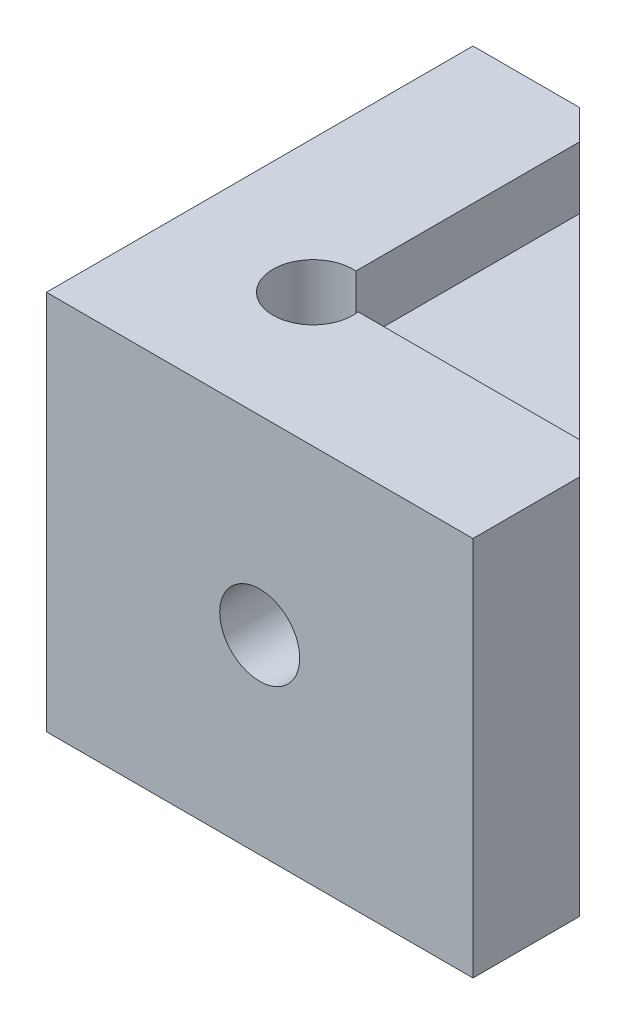
SolidWorks part; units mm, degrees
ref_plane "Front Plane" through (0, 0, 0) normal (0, 0, 1) x (1, 0, 0)
ref_plane "Top Plane" through (0, 0, 0) normal (0, 1, 0) x (1, 0, 0)
ref_plane "Right Plane" through (0, 0, 0) normal (1, 0, 0) x (0, 0, -1)
sketch "Sketch1" plane through (0, 0, 0) normal (0, 1, 0) x (1, 0, 0)
  line L1 (0, 0) -> (38.1, 0)
  line L5 (0, 0) -> (0, 38.1)
  line L6 (0, 38.1) -> (9.525, 38.1)
  line L7 (9.525, 38.1) -> (38.1, 9.525)
  line L8 (38.1, 9.525) -> (38.1, 0)
  dimension "D1" = 38.1
  dimension "D2" = 9.525
extrude "Main Body" add sketch "Sketch1" along normal blind 34
sketch "Sketch3" plane through (0, 0, 0) normal (0, 0, 1) x (1, 0, 0)
  line L0 (0, 0) -> (38.1, 34) construction
  circle A0 centre (19.05, 17) radius 3.5719
  circle A1 centre (19.05, 17) radius 7.9375 construction
  dimension "D1" = 7.1437
  dimension "D2" = 15.875
extrude "9/32 Right Rail" cut sketch "Sketch3" against normal blind 5.5562 and the other way through all
sketch "Sketch4" plane through (0, 0, 0) normal (-1, 0, 0) x (0, 0, 1)
  line L0 (0, 0) -> (-38.1, 34) construction
  circle A0 centre (-19.05, 17) radius 3.5719
  circle A1 centre (-19.05, 17) radius 7.9375 construction
  dimension "D1" = 7.1437
  dimension "D2" = 15.875
extrude "9/32 Left Rail" cut sketch "Sketch4" against normal blind 5.5562
sketch "Sketch8" plane through (0, 34, 0) normal (0, 1, 0) x (1, 0, 0)
  line L0 (0, 0) -> (23.8125, 23.8125) construction
  line L1 (38.1, 9.525) -> (9.525, 38.1) construction
  circle A0 centre (11.9062, 11.9062) radius 3.175 construction
  circle A1 centre (11.9062, 11.9062) radius 7.9375 construction
  circle A2 centre (11.9062, 11.9062) radius 3.5719
  dimension "D1" = 6.35
  dimension "D2" = 15.875
  dimension "D3" = 0.3969
extrude "9/32 Topper" cut sketch "Sketch8" against normal through all both and the other way through all
ref_plane "Plane1" through (5.5562, 0, 0) normal (-1, 0, 0) x (0, 0, 1)
sketch "Sketch9" plane through (0, 0, 0) normal (-1, 0, 0) x (0, 0, 1)
  line L0 (-19.05, 0) -> (-19.05, 34) construction
  line L1 (-12.6342, 17) -> (-15.8421, 22.5562) construction
  line L2 (-15.8421, 22.5562) -> (-22.2579, 22.5562) construction
  line L3 (-22.2579, 22.5562) -> (-25.4658, 17) construction
  line L4 (-25.4658, 17) -> (-22.2579, 11.4437) construction
  line L5 (-22.2579, 11.4437) -> (-15.8421, 11.4437) construction
  line L6 (-15.8421, 11.4437) -> (-12.6342, 17) construction
  line L7 (-38.1, 0) -> (0, 0) construction
  line L8 (-38.1, 34) -> (0, 34) construction
  line L9 (-22.3725, 22.7547) -> (-25.6949, 17)
  line L10 (-25.6949, 17) -> (-22.3725, 11.2453)
  line L11 (-22.3725, 11.2453) -> (-15.7275, 11.2453)
  line L12 (-15.7275, 11.2453) -> (-12.4051, 17)
  line L13 (-12.4051, 17) -> (-15.7275, 22.7547)
  line L14 (-15.7275, 22.7547) -> (-22.3725, 22.7547)
  line L15 (-38.1, 27.65) -> (-38.1, 6.35) construction
  line L16 (-38.1, 34) -> (-38.1, 0) construction
  line L17 (-38.1, 6.35) -> (-5.5562, 6.35) construction
  line L18 (-5.5562, 6.35) -> (-5.5562, 27.65) construction
  line L19 (-5.5562, 27.65) -> (-38.1, 27.65) construction
  line L20 (0, 34) -> (0, 0) construction
  circle A0 centre (-19.05, 17) radius 5.5563 construction
  point P15 (-19.05, 17)
  point P27 (-38.1, 17)
  point P29 (-38.1, 17)
  dimension "D1" = 11.1125
  dimension "D3" = 5.5562
  dimension "D4" = 6.35
  dimension "D2" = 0.1984
extrude "Cut-Extrude3" cut sketch "Sketch9" against normal up to surface (32.5438 mm away) from surface at -5.5563 up to face at (38.1, 17, -4.7625) starting at plane "Plane1"
ref_plane "Plane2" through (0, 0, -5.5563) normal (0, 0, 1) x (1, 0, 0)
sketch "Sketch10" plane through (0, 0, 0) normal (0, 0, 1) x (1, 0, 0)
  line L0 (19.05, 0) -> (19.05, 34) construction
  line L1 (0, 0) -> (38.1, 0) construction
  line L2 (0, 34) -> (38.1, 34) construction
  line L3 (15.613, 22.9531) -> (12.1759, 17)
  line L4 (25.4658, 17) -> (22.2579, 22.5562) construction
  line L5 (22.2579, 22.5562) -> (15.8421, 22.5562) construction
  line L6 (15.8421, 22.5562) -> (12.6342, 17) construction
  line L13 (12.6342, 17) -> (15.8421, 11.4437) construction
  line L14 (15.8421, 11.4437) -> (22.2579, 11.4437) construction
  line L15 (22.2579, 11.4437) -> (25.4658, 17) construction
  line L16 (12.1759, 17) -> (15.613, 11.0469)
  line L17 (15.613, 11.0469) -> (22.487, 11.0469)
  line L18 (22.487, 11.0469) -> (25.9241, 17)
  line L19 (25.9241, 17) -> (22.487, 22.9531)
  line L20 (22.487, 22.9531) -> (15.613, 22.9531)
  circle A0 centre (19.05, 17) radius 5.5563 construction
  dimension "D1" = 11.1125
  dimension "D2" = 0.3969
extrude "Cut-Extrude4" cut sketch "Sketch10" against normal up to surface (32.5438 mm away) from surface at -5.5563 up to face at (4.7625, 17, -38.1) starting at plane "Plane2"
sketch "Sketch13" plane through (0, 34, 0) normal (0, 1, 0) x (1, 0, 0)
  line L0 (35.2199, 12.4051) -> (25.9241, 12.4051) construction
  line L1 (12.1759, 35.4491) -> (12.1759, 25.6949) construction
  line L2 (35.2199, 12.4051) -> (12.1759, 12.4051)
  line L3 (12.1759, 35.4491) -> (12.1759, 12.4051)
  line L4 (35.2199, 12.4051) -> (12.1759, 35.4491)
extrude "Cut-Extrude6" cut sketch "Sketch13" against normal blind 5.5562
